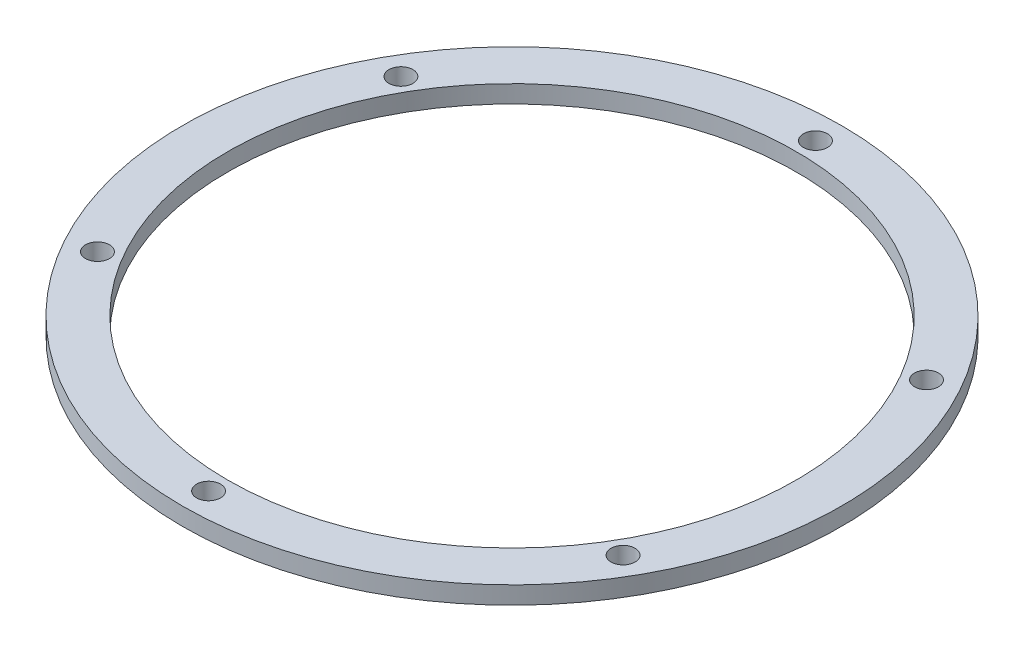
SolidWorks part; units mm, degrees
ref_plane "Front Plane" through (0, 0, 0) normal (0, 0, 1) x (1, 0, 0)
ref_plane "Top Plane" through (0, 0, 0) normal (0, 1, 0) x (1, 0, 0)
ref_plane "Right Plane" through (0, 0, 0) normal (1, 0, 0) x (0, 0, -1)
sketch "Sketch1" plane through (0, 0, 0) normal (0, 1, 0) x (1, 0, 0)
  circle A0 centre (0, 0) radius 51.181
  circle A1 centre (0, 0) radius 59.309
  dimension "D1" = 118.618
  dimension "D2" = 102.362
extrude "Boss-Extrude1" add sketch "Sketch1" along normal blind 3.175
sketch "Sketch2" plane through (0, 3.175, 0) normal (0, 1, 0) x (1, 0, 0)
  line L0 (0, 0) -> (0, 54.61) construction
  circle A0 centre (0, 0) radius 54.61 construction
  circle A1 centre (0, 54.61) radius 2.159
  dimension "D1" = 109.22
extrude "Cut-Extrude1" cut sketch "Sketch2" against normal up to next (3.175 mm away)
pattern_circular "CirPattern1" count 6 over 360 about axis through (0, 0, 0) along (0, 1, 0) of "Cut-Extrude1"
